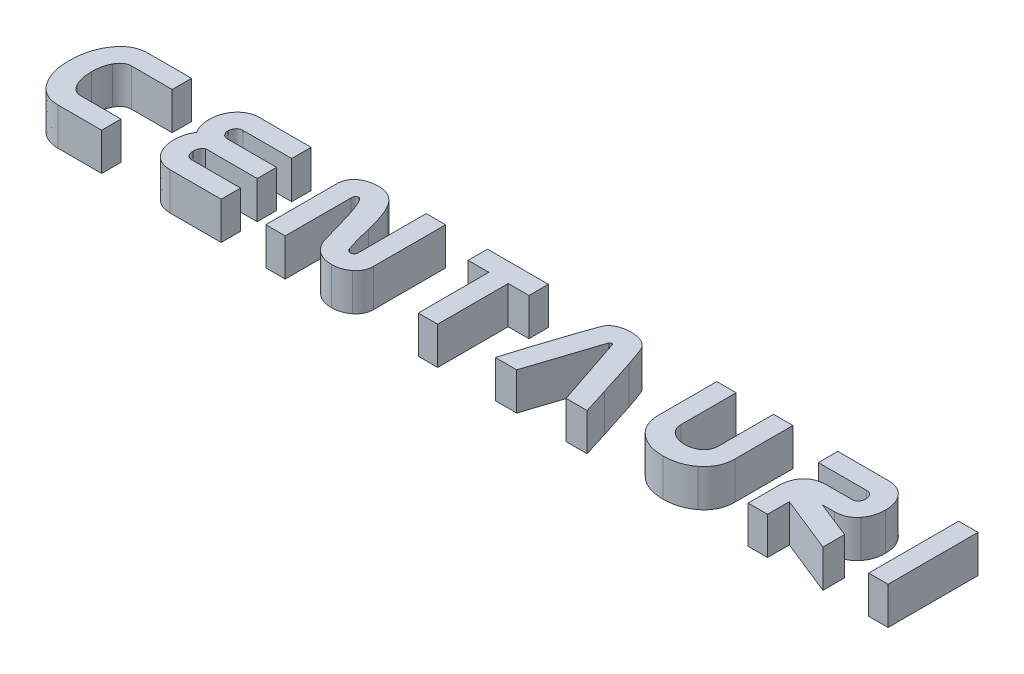
SolidWorks part; units mm, degrees
ref_plane "Front Plane" through (0, 0, 0) normal (0, 0, 1) x (1, 0, 0)
ref_plane "Top Plane" through (0, 0, 0) normal (0, 1, 0) x (1, 0, 0)
ref_plane "Right Plane" through (0, 0, 0) normal (1, 0, 0) x (0, 0, -1)
sketch "Sketch2" plane through (0, 0, 0) normal (0, 1, 0) x (1, 0, 0)
  text T0 "CENTAURI" font "Nasa" height 12
extrude "Boss-Extrude1" add sketch "Sketch2" along normal blind 5
